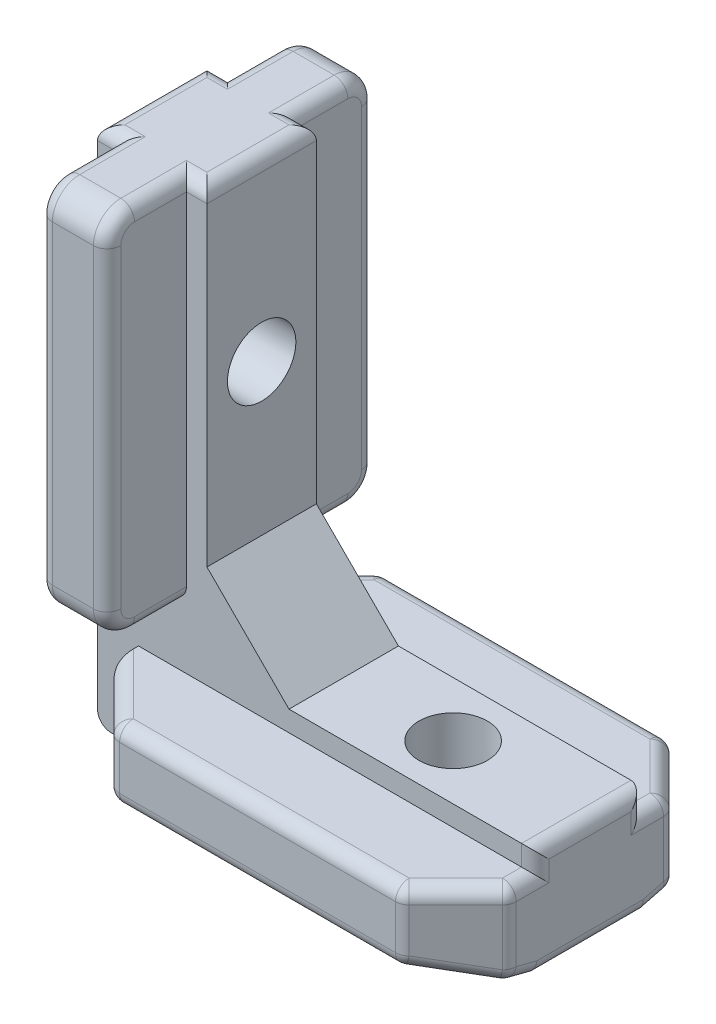
SolidWorks part; units mm, degrees
other "Camera1"
material "Stainless Steel (ferritic)"
ref_plane "Front Plane" through (0, 0, 0) normal (0, 0, 1) x (1, 0, 0)
ref_plane "Top Plane" through (0, 0, 0) normal (0, 1, 0) x (1, 0, 0)
ref_plane "Right Plane" through (0, 0, 0) normal (1, 0, 0) x (0, 0, -1)
sketch "Sketch1" plane through (0, 0, 0) normal (0, 0, 1) x (1, 0, 0)
  line L0 (0, 0) -> (0, 38)
  line L1 (0, 38) -> (8, 38)
  line L2 (8, 38) -> (8, 8)
  line L3 (8, 8) -> (32, 8)
  line L4 (32, 8) -> (32, 0)
  line L5 (32, 0) -> (0, 0)
  dimension "D1" = 8
  dimension "D2" = 8
  dimension "D3" = 32
  dimension "D4" = 38
extrude "Boss-Extrude1" add sketch "Sketch1" along normal mid plane 8
sketch "Sketch2" plane through (32, 0, 0) normal (1, 0, 0) x (0, 0, -1)
  line L0 (-4, 6.5) -> (-9.8, 6.5)
  line L1 (-4, 0) -> (-4, 8) construction
  line L2 (-9.8, 6.5) -> (-9.8, 1.5)
  line L3 (-9.8, 1.5) -> (-4, 0)
  line L4 (-4, 0) -> (-4, 6.5)
  line L6 (4, 0) -> (4, 6.5)
  line L7 (4, 6.5) -> (9.8, 6.5)
  line L8 (9.8, 6.5) -> (9.8, 1.5)
  line L9 (9.8, 1.5) -> (4, 0)
  line L11 (-4, 8) -> (4, 8) construction
  point P13 (0, 0)
  dimension "D1" = 1.5
  dimension "D2" = 19.6
  dimension "D3" = 5
extrude "Boss-Extrude2" add sketch "Sketch2" against normal blind 29
chamfer "Chamfer1" distance 4 angle 45 4 edges at (32, 4, -9.8) (32, 4, 9.8) (3, 4, -9.8) (3, 4, 9.8)
chamfer "Chamfer2" distance 6 angle 45 1 edges at (8, 8, 0)
sketch "Sketch3" plane through (0, 0, 0) normal (0, -1, 0) x (1, 0, 0)
  line L0 (0, 4) -> (0, -4) construction
  line L1 (0, 0) -> (22.2253, 0) construction
  circle A0 centre (22, 0) radius 2.5
  dimension "D2" = 5
  dimension "D1" = 22
extrude "Cut-Extrude1" cut sketch "Sketch3" against normal up to next
sketch "Sketch4" plane through (0, 0, 0) normal (-1, 0, 0) x (0, 0, 1)
  line L0 (0, 0) -> (0, 38) construction
  line L1 (4, 38) -> (-4, 38) construction
  line L2 (4, 0) -> (-4, 0) construction
  circle A0 centre (0, 25) radius 2.5
  dimension "D1" = 5
  dimension "D2" = 25
extrude "Cut-Extrude2" cut sketch "Sketch4" against normal up to next
sketch "Sketch5" plane through (0, 38, 0) normal (0, 1, 0) x (1, 0, 0)
  line L0 (1.5, 4) -> (1.5, 9.8)
  line L1 (8, 4) -> (0, 4) construction
  line L2 (1.5, 9.8) -> (6.5, 9.8)
  line L3 (6.5, 9.8) -> (6.5, 4)
  line L4 (3, 4) -> (32, 4) construction
  line L5 (7, 9.8) -> (28, 9.8) construction
  line L6 (3, -4) -> (32, -4) construction
  line L7 (6.5, -4) -> (6.5, -9.8)
  line L8 (6.5, -9.8) -> (1.5, -9.8)
  line L9 (1.5, -9.8) -> (1.5, -4)
  line L10 (8, -4) -> (0, -4) construction
  line L11 (1.5, -4) -> (6.5, -4)
  line L12 (1.5, 4) -> (6.5, 4)
  line L13 (8, -4) -> (8, 4) construction
  dimension "D1" = 1.5
  dimension "D2" = 5
extrude "Boss-Extrude3" add sketch "Sketch5" against normal blind 27
fillet "Fillet1" radius 2 4 edges at (4, 11, -9.8) (4, 11, 9.8) (4, 38, -9.8) (4, 38, 9.8)
fillet "Fillet2" radius 1 55 edges at (6.5, 11, -5.9) (6.5, 11.5858, -9.2142) (6.5, 38, -5.9) (6.5, 37.4142, -9.2142) (1.5, 11, -5.9) (1.5, 11.5858, -9.2142) (1.5, 38, -5.9) (1.5, 37.4142, -9.2142) (6.5, 11, 5.9) (6.5, 11.5858, 9.2142) (6.5, 38, 5.9) (6.5, 37.4142, 9.2142) (1.5, 11, 5.9) (1.5, 11.5858, 9.2142) (1.5, 38, 5.9) (1.5, 37.4142, 9.2142) (6.5, 24.5, -9.8) (1.5, 24.5, -9.8) (6.5, 24.5, 9.8) (1.5, 24.5, 9.8) (32, 0, 0) (32, 0.2328, 4.9) (32, 3.4828, 5.8) (32, 6.5, 4.9) (32, 7.25, 4) (32, 8, 0) (32, 7.25, -4) (32, 6.5, -4.9) (32, 3.4828, -5.8) (32, 0.2328, -4.9) (7.25, 38, -4) (8, 38, 0) (7.25, 38, 4) (0.75, 38, 4) (0, 38, 0) (0.75, 38, -4) (30, 0.9828, 7.8) (30, 6.5, 7.8) (28, 4, 9.8) (17.5, 1.5, 9.8) (17.5, 6.5, 9.8) (7, 4, 9.8) (5, 0.9828, 7.8) (3, 3.4828, 5.8) (5, 6.5, 7.8) (5, 6.5, -7.8) (3, 3.4828, -5.8) (5, 0.9828, -7.8) (30, 6.5, -7.8) (30, 0.9828, -7.8) (28, 4, -9.8) (17.5, 6.5, -9.8) (7, 4, -9.8) (17.5, 1.5, -9.8) (0, 0, 0)
